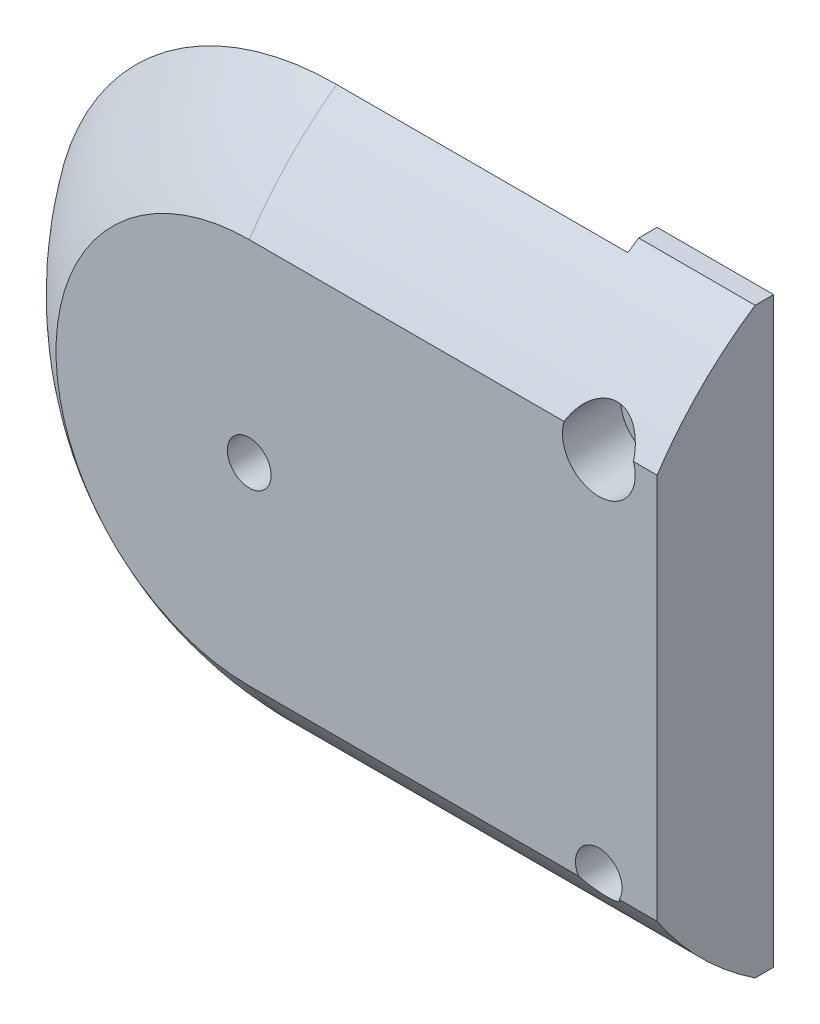
SolidWorks part; units mm, degrees
ref_plane "Front Plane" through (0, 0, 0) normal (0, 0, 1) x (1, 0, 0)
ref_plane "Top Plane" through (0, 0, 0) normal (0, 1, 0) x (1, 0, 0)
ref_plane "Right Plane" through (0, 0, 0) normal (1, 0, 0) x (0, 0, -1)
sketch "Sketch1" plane through (0, 0, 0) normal (0, 0, 1) x (1, 0, 0)
  line L0 (0, 10) -> (14, 10)
  line L1 (14, 10) -> (14, -10)
  line L2 (14, -10) -> (0, -10)
  circle A0 centre (0, 0) radius 10
extrude "Boss-Extrude1" add sketch "Sketch1" against normal blind 4 contours A0 | A0 L2 L1 L0
sketch "Sketch2" plane through (0, 0, 0) normal (0, 0, 1) x (1, 0, 0)
  line L0 (0, 10) -> (10, 10)
  line L1 (0, 10) -> (14, 10) construction
  line L2 (10, 10) -> (10, 0)
  line L3 (0, -10) -> (10, -10)
  line L4 (14, -10) -> (0, -10) construction
  line L5 (10, -10) -> (10, 0)
  circle A0 centre (0, 0) radius 10
extrude "Body Hole" cut sketch "Sketch2" against normal blind 2 from offset 3 contours A0 | A0 L2 L0 | A0 L3 L5 offset against normal yes
sketch "Sketch11" plane through (0, 0, 0) normal (0, 0, 1) x (1, 0, 0)
  circle A0 centre (0, 0) radius 2
extrude "Boss-Extrude2" add sketch "Sketch11" against normal blind 2 from offset 3 offset against normal yes
sketch "Sketch4" plane through (0, 0, 0) normal (0, 0, 1) x (1, 0, 0)
  circle A0 centre (0, 0) radius 0.75
extrude "Cut-Extrude2" cut sketch "Sketch4" against normal through all
sketch "Sketch3" plane through (0, 0, 0) normal (0, 0, 1) x (1, 0, 0)
  line L1 (10, 0) -> (12, 0) construction
  line L2 (12, 0) -> (12, 6.25) construction
  line L3 (12, 0) -> (12, -6.25) construction
  circle A1 centre (12, 6.25) radius 0.8
  circle A2 centre (12, -6.25) radius 0.8
extrude "Screw Holes" cut sketch "Sketch3" against normal through all
sketch "Sketch6" plane through (0, 0, 0) normal (0, 0, 1) x (1, 0, 0)
  circle A0 centre (12, 6.25) radius 1.25
extrude "Screw Heads" cut sketch "Sketch6" against normal blind 2
sketch "Sketch9" plane through (0, 0, 0) normal (1, 0, 0) x (0, 0, -1)
  line L0 (0, 0) -> (10, 0) construction
  line L1 (10, 0) -> (-2, 0) construction
  line L2 (-2, 0) -> (-2, 12)
  line L3 (-2, 12) -> (10, 12)
  line L4 (-2, 0) -> (-2, 2.75) construction
  line L5 (-2, 2.75) -> (-1.6806, 2.75)
  arc A0 (10, 12) -> (-2, 0) centre (10, 0) ccw
revolve "Cut-Revolve1" cut sketch "Sketch9" angle 180 about L0
sketch "Sketch10" plane through (0, 0, 0) normal (1, 0, 0) x (0, 0, -1)
  line L0 (0, 0) -> (10, 0) construction
  line L1 (0, 6.6332) -> (0, -6.6332) construction
  line L2 (10, 0) -> (-2, 0) construction
  line L3 (-2, 0) -> (-2, 12)
  line L4 (-2, 12) -> (10, 12)
  line L5 (-2, 0) -> (-2, -12)
  line L6 (-2, -12) -> (10, -12)
  arc A0 (10, 12) -> (-2, 0) centre (10, 0) ccw
  arc A1 (-2, 0) -> (10, -12) centre (10, 0) ccw
extrude "Cut-Extrude1" cut sketch "Sketch10" along normal through all contours A0 L4 L3 | A1 L5 L6
